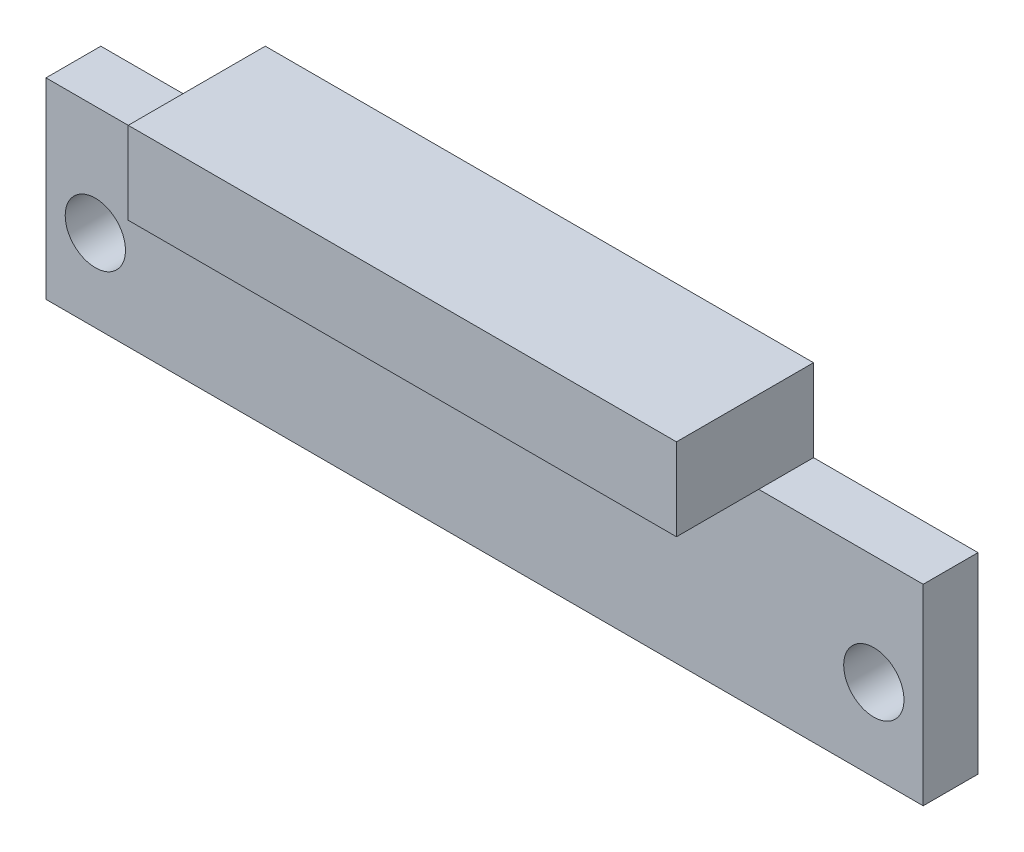
SolidWorks part; units mm, degrees
ref_plane "前视基准面" through (0, 0, 0) normal (0, 0, 1) x (1, 0, 0)
ref_plane "上视基准面" through (0, 0, 0) normal (0, 1, 0) x (1, 0, 0)
ref_plane "右视基准面" through (0, 0, 0) normal (1, 0, 0) x (0, 0, -1)
sketch "草图1" plane through (0, 0, 0) normal (0, 0, 1) x (1, 0, 0)
  line L1 (0, 0) -> (32, 0)
  line L2 (0, 0) -> (0, 7)
  line L3 (0, 7) -> (32, 7)
  line L4 (32, 0) -> (32, 7)
  dimension "D1" = 32
  dimension "D2" = 7
extrude "凸台-拉伸1" add sketch "草图1" along normal blind 2
sketch "草图2" plane through (0, 0, 0) normal (0, 0, -1) x (-1, 0, 0)
  line L0 (-32, 7) -> (0, 7) construction
  line L1 (-32, 0) -> (-32, 7) construction
  circle A0 centre (-30.2, 3) radius 1.1
  circle A1 centre (-1.8, 3) radius 1.1
  dimension "D1" = 2.2
  dimension "D2" = 2.2
  dimension "D3" = 4
  dimension "D4" = 4
  dimension "D5" = 28.4
  dimension "D6" = 1.8
extrude "切除-拉伸1" cut sketch "草图2" against normal blind 2
sketch "草图3" plane through (0, 0, 0) normal (0, 0, -1) x (-1, 0, 0)
  line L0 (-32, 7) -> (0, 7) construction
  line L1 (-26, 7) -> (-6, 7)
  line L2 (-26, 7) -> (-26, 10)
  line L3 (-26, 10) -> (-6, 10)
  line L4 (-6, 7) -> (-6, 10)
  line L5 (-32, 0) -> (-32, 7) construction
  dimension "D1" = 3
  dimension "D2" = 20
  dimension "D3" = 6
extrude "凸台-拉伸2" add sketch "草图3" against normal blind 5
